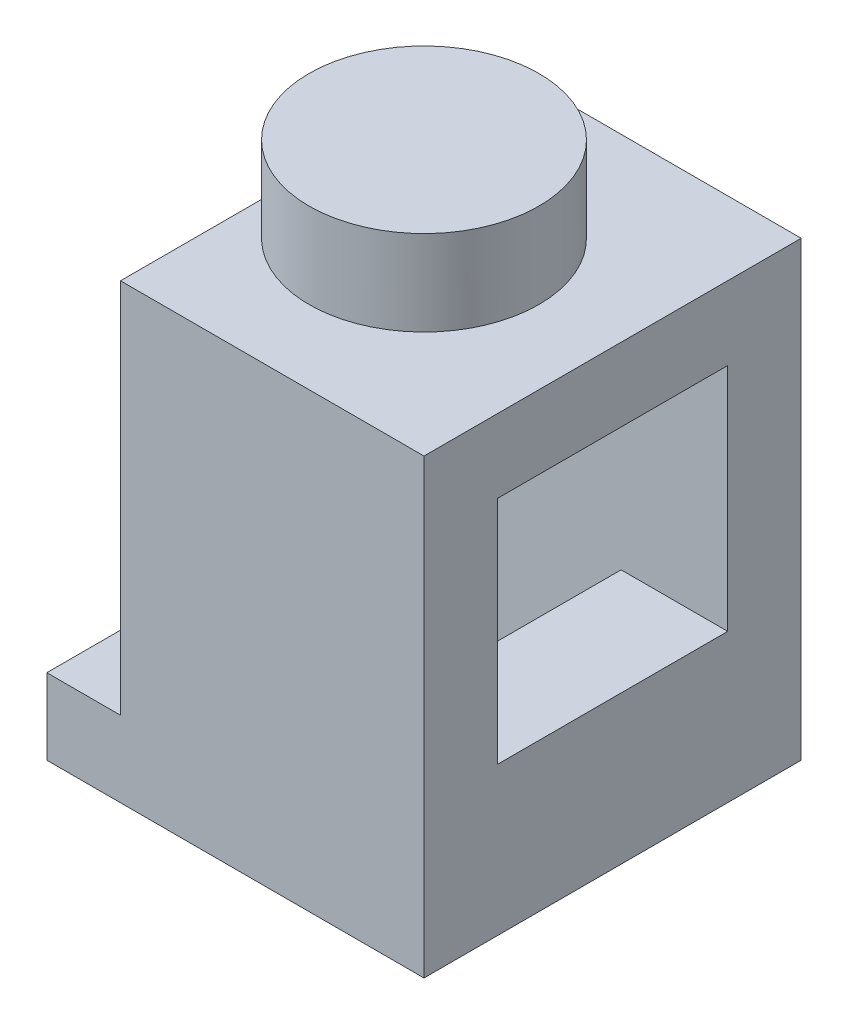
SolidWorks part; units mm, degrees
ref_plane "Front Plane" through (0, 0, 0) normal (0, 0, 1) x (1, 0, 0)
ref_plane "Top Plane" through (0, 0, 0) normal (0, 1, 0) x (1, 0, 0)
ref_plane "Right Plane" through (0, 0, 0) normal (1, 0, 0) x (0, 0, -1)
sketch "Sketch1" plane through (0, 0, 0) normal (0, 1, 0) x (1, 0, 0)
  line L1 (-3.98, 3.98) -> (3.98, 3.98)
  line L2 (-3.98, 3.98) -> (-3.98, -3.98)
  line L3 (-3.98, -3.98) -> (3.98, -3.98)
  line L4 (3.98, 3.98) -> (3.98, -3.98)
  line L5 (-3.98, 3.98) -> (3.98, -3.98) construction
  line L6 (-3.98, -3.98) -> (3.98, 3.98) construction
  point P0 (0, 0)
  dimension "D1" = 7.96
extrude "Extrude1" add sketch "Sketch1" along normal blind 9.54
sketch "Sketch2" plane through (0, 9.54, 0) normal (0, 1, 0) x (1, 0, 0)
  circle A0 centre (0, 0) radius 2.425
  dimension "D1" = 4.85
extrude "Extrude2" add sketch "Sketch2" along normal blind 1.8
shell "Shell1" thickness 1.55
sketch "Sketch3" plane through (0, 7.99, 0) normal (0, -1, 0) x (1, 0, 0)
  line L0 (2.43, -2.43) -> (-2.43, -2.43) construction
  line L1 (-2.43, -2.43) -> (-2.43, 2.43) construction
  line L2 (-2.43, 2.43) -> (2.43, 2.43) construction
  line L3 (2.43, 2.43) -> (2.43, -2.43) construction
  line L4 (2.43, -2.43) -> (-2.43, -2.43)
  line L5 (-2.43, -2.43) -> (-2.43, 2.43)
  line L6 (-2.43, 2.43) -> (2.43, 2.43)
  line L7 (2.43, 2.43) -> (2.43, -2.43)
extrude "Extrude3" cut sketch "Sketch3" against normal blind 0.14
sketch "Sketch5" plane through (0, 9.54, 0) normal (0, 1, 0) x (1, 0, 0)
  line L0 (-3.98, -3.98) -> (3.98, -3.98) construction
  line L1 (-3.98, 3.98) -> (-2.425, 3.98)
  line L2 (-3.98, 3.98) -> (-3.98, -3.98)
  line L3 (-3.98, -3.98) -> (-2.425, -3.98)
  line L4 (-2.425, 3.98) -> (-2.425, -3.98)
  circle A0 centre (0, 0) radius 2.425 construction
  point P7 (-2.425, 0)
extrude "Extrude5" cut sketch "Sketch5" against normal blind 7.94
sketch "Sketch7" plane through (0, 8.13, 0) normal (0, -1, 0) x (1, 0, 0)
  line L0 (2.43, -2.43) -> (-2.43, -2.43) construction
  line L1 (-2.425, 2.43) -> (-1.725, 2.43)
  line L2 (-2.425, 2.43) -> (-2.425, -2.43)
  line L3 (-2.425, -2.43) -> (-1.725, -2.43)
  line L4 (-1.725, 2.43) -> (-1.725, -2.43)
  line L5 (-2.425, -2.43) -> (2.43, -2.43) construction
  line L6 (2.43, 2.43) -> (1.73, 2.43)
  line L7 (2.43, 2.43) -> (2.43, -2.43)
  line L8 (2.43, -2.43) -> (1.73, -2.43)
  line L9 (1.73, 2.43) -> (1.73, -2.43)
  line L10 (3.98, 3.98) -> (3.98, -3.98) construction
  dimension "D1" = 2.25
extrude "Extrude6" add sketch "Sketch7" along normal up to surface (6.53 mm away) up to face at (-2.815, 1.6, 0)
sketch "Sketch4" plane through (3.98, 0, 0) normal (1, 0, 0) x (0, 0, -1)
  line L0 (-3.98, 9.54) -> (3.98, 9.54) construction
  line L1 (-2.43, 7.99) -> (2.43, 7.99)
  line L2 (-2.43, 7.99) -> (-2.43, 3.13)
  line L3 (-2.43, 3.13) -> (2.43, 3.13)
  line L4 (2.43, 7.99) -> (2.43, 3.13)
  line L5 (3.98, 9.54) -> (3.98, 0) construction
  line L6 (-3.98, 9.54) -> (-3.98, 0) construction
  dimension "D1" = 1.55
  dimension "D2" = 1.55
  dimension "D3" = 1.55
extrude "Extrude7" cut sketch "Sketch4" against normal up to next
sketch "Sketch8" plane through (-2.425, 0, 0) normal (-1, 0, 0) x (0, 0, 1)
  line L0 (2.43, 7.99) -> (2.43, 3.13) construction
  line L1 (-2.43, 7.99) -> (2.43, 7.99) construction
  line L2 (-2.43, 3.13) -> (-2.43, 7.99) construction
  line L3 (2.43, 3.13) -> (-2.43, 3.13) construction
  line L4 (2.43, 7.99) -> (2.43, 3.13) construction
  line L5 (-2.43, 7.99) -> (2.43, 7.99) construction
  line L6 (-2.43, 3.13) -> (-2.43, 7.99) construction
  line L7 (2.43, 3.13) -> (-2.43, 3.13) construction
  circle A0 centre (0, 5.56) radius 2.425
  point P6 (2.43, 5.56)
  point P7 (0, 7.99)
  dimension "D1" = 4.85
extrude "Extrude8" add sketch "Sketch8" along normal up to surface (1.555 mm away) up to face at (-3.98, 0.8, 0)
sketch "Sketch9" plane through (-3.98, 0, 0) normal (-1, 0, 0) x (0, 0, 1)
  circle A0 centre (0, 5.56) radius 1.565
  circle A1 centre (0, 5.56) radius 2.425 construction
  dimension "D1" = 0.86
extrude "Extrude9" cut sketch "Sketch9" against normal through all
